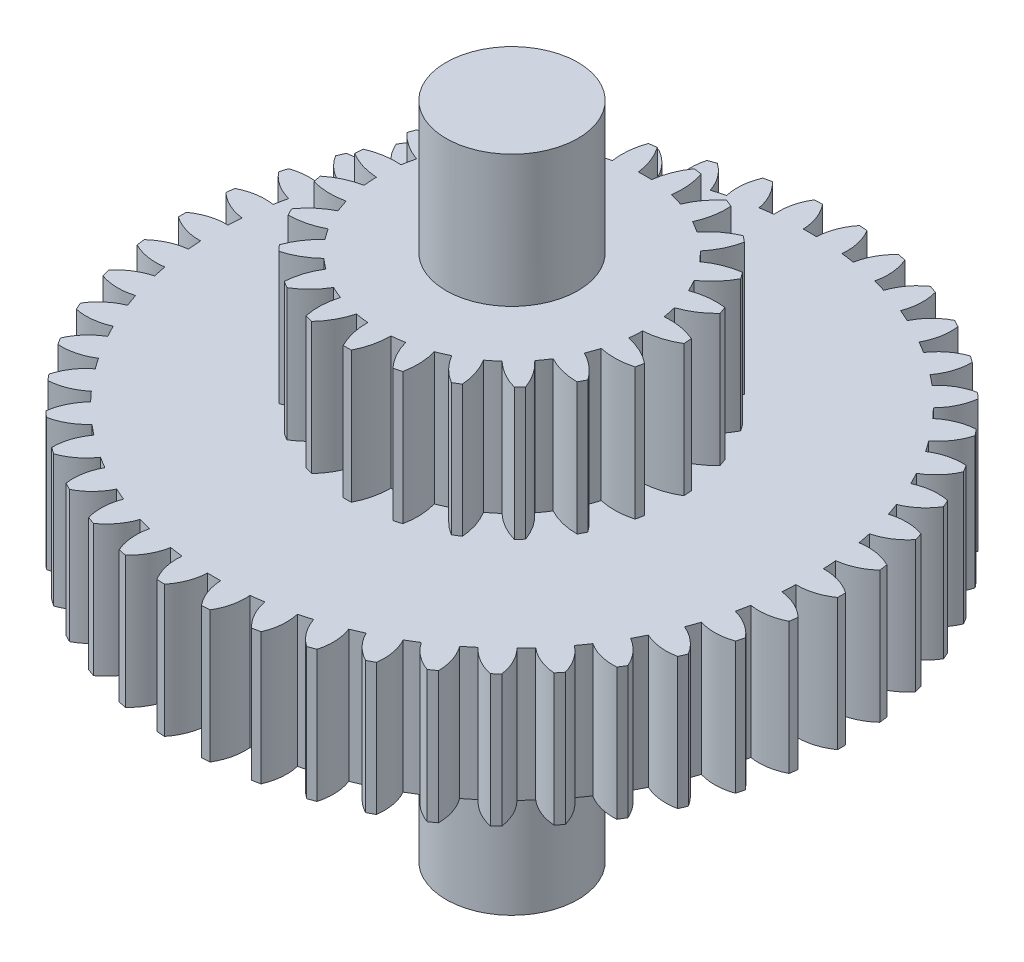
SolidWorks part; units mm, degrees
ref_plane "Front Plane" through (0, 0, 0) normal (0, 0, 1) x (1, 0, 0)
ref_plane "Top Plane" through (0, 0, 0) normal (0, 1, 0) x (1, 0, 0)
ref_plane "Right Plane" through (0, 0, 0) normal (1, 0, 0) x (0, 0, -1)
sketch "Sketch1" plane through (0, 0, 0) normal (0, 1, 0) x (1, 0, 0)
  arc A0 (-1.1228, 2.2337) -> (-1.1773, 2.2054) centre (0, 0) ccw
  arc A1 (-2.1122, 0.8038) -> (-2.1457, 0.7095) centre (0, 0) ccw
  arc A2 (0.05, 2.2594) -> (0.14, 2.4961) centre (0.4546, 2.241) cw
  arc A3 (-0.05, 2.2594) -> (-0.14, 2.4961) centre (-0.4546, 2.241) ccw
  arc A4 (0.3572, 2.2316) -> (0.4786, 2.4538) centre (0.7555, 2.1582) cw
  arc A5 (0.2581, 2.2452) -> (0.2012, 2.4919) centre (-0.1453, 2.282) ccw
  arc A6 (0.6577, 2.1622) -> (0.8082, 2.3657) centre (1.0424, 2.0352) cw
  arc A7 (0.5614, 2.1892) -> (0.5386, 2.4413) centre (0.1668, 2.2805) ccw
  arc A8 (0.946, 2.0525) -> (1.1228, 2.2337) centre (1.3098, 1.8743) cw
  arc A9 (0.8543, 2.0923) -> (0.866, 2.3452) centre (0.4758, 2.2366) ccw
  arc A10 (1.2167, 1.9045) -> (1.4165, 2.06) centre (1.5528, 1.6785) cw
  arc A11 (1.1313, 1.9565) -> (1.1773, 2.2054) centre (0.7759, 2.151) ccw
  arc A12 (1.4647, 1.7211) -> (1.6838, 1.8479) centre (1.7669, 1.4514) cw
  arc A13 (1.3871, 1.7842) -> (1.4666, 2.0246) centre (1.0616, 2.0253) ccw
  arc A14 (1.6854, 1.5057) -> (1.9198, 1.6014) centre (1.9481, 1.1973) cw
  arc A15 (1.6172, 1.5787) -> (1.7287, 1.806) centre (1.3275, 1.8619) ccw
  arc A16 (1.8747, 1.2621) -> (2.12, 1.3251) centre (2.093, 0.9209) cw
  arc A17 (1.8171, 1.3438) -> (1.9585, 1.5538) centre (1.5686, 1.6638) ccw
  arc A18 (2.0291, 0.9951) -> (2.2806, 1.0241) centre (2.1989, 0.6273) cw
  arc A19 (1.9831, 1.0839) -> (2.1518, 1.2727) centre (1.7806, 1.4347) ccw
  arc A20 (2.1457, 0.7095) -> (2.3988, 0.704) centre (2.2638, 0.3221) cw
  arc A21 (2.1122, 0.8038) -> (2.3051, 0.9678) centre (1.9593, 1.1788) ccw
  arc A22 (2.2224, 0.4107) -> (2.4724, 0.3708) centre (2.2866, 0.0108) cw
  arc A23 (2.202, 0.5087) -> (2.4154, 0.6449) centre (2.1016, 0.9011) ccw
  arc A24 (2.2576, 0.1043) -> (2.4998, 0.0307) centre (2.2668, -0.3006) cw
  arc A25 (2.2508, 0.2041) -> (2.4807, 0.31) centre (2.2047, 0.6065) ccw
  arc A26 (2.2508, -0.2041) -> (2.4807, -0.31) centre (2.2047, -0.6065) cw
  arc A27 (2.2576, -0.1043) -> (2.4998, -0.0307) centre (2.2668, 0.3006) ccw
  arc A28 (2.202, -0.5087) -> (2.4154, -0.6449) centre (2.1016, -0.9011) cw
  arc A29 (2.2224, -0.4107) -> (2.4724, -0.3708) centre (2.2866, -0.0108) ccw
  arc A30 (2.1122, -0.8038) -> (2.3051, -0.9678) centre (1.9593, -1.1788) cw
  arc A31 (2.1457, -0.7095) -> (2.3988, -0.704) centre (2.2638, -0.3221) ccw
  arc A32 (1.9831, -1.0839) -> (2.1518, -1.2727) centre (1.7806, -1.4347) cw
  arc A33 (2.0291, -0.9951) -> (2.2806, -1.0241) centre (2.1989, -0.6273) ccw
  arc A34 (1.8171, -1.3438) -> (1.9585, -1.5538) centre (1.5686, -1.6638) cw
  arc A35 (1.8747, -1.2621) -> (2.12, -1.3251) centre (2.093, -0.9209) ccw
  arc A36 (1.6172, -1.5787) -> (1.7287, -1.806) centre (1.3275, -1.8619) cw
  arc A37 (1.6854, -1.5057) -> (1.9198, -1.6014) centre (1.9481, -1.1973) ccw
  arc A38 (1.3871, -1.7842) -> (1.4666, -2.0246) centre (1.0616, -2.0253) cw
  arc A39 (1.4647, -1.7211) -> (1.6838, -1.8479) centre (1.7669, -1.4514) ccw
  arc A40 (1.1313, -1.9565) -> (1.1773, -2.2054) centre (0.7759, -2.151) cw
  arc A41 (1.2167, -1.9045) -> (1.4165, -2.06) centre (1.5528, -1.6785) ccw
  arc A42 (0.8543, -2.0923) -> (0.866, -2.3452) centre (0.4758, -2.2366) cw
  arc A43 (0.946, -2.0525) -> (1.1228, -2.2337) centre (1.3098, -1.8743) ccw
  arc A44 (0.5614, -2.1892) -> (0.5386, -2.4413) centre (0.1668, -2.2805) cw
  arc A45 (0.6577, -2.1622) -> (0.8082, -2.3657) centre (1.0424, -2.0352) ccw
  arc A46 (0.2581, -2.2452) -> (0.2012, -2.4919) centre (-0.1453, -2.282) cw
  arc A47 (0.3572, -2.2316) -> (0.4786, -2.4538) centre (0.7555, -2.1582) ccw
  arc A48 (-0.05, -2.2594) -> (-0.14, -2.4961) centre (-0.4546, -2.241) cw
  arc A49 (0.05, -2.2594) -> (0.14, -2.4961) centre (0.4546, -2.241) ccw
  arc A50 (-0.3572, -2.2316) -> (-0.4786, -2.4538) centre (-0.7555, -2.1582) cw
  arc A51 (-0.2581, -2.2452) -> (-0.2012, -2.4919) centre (0.1453, -2.282) ccw
  arc A52 (-0.6577, -2.1622) -> (-0.8082, -2.3657) centre (-1.0424, -2.0352) cw
  arc A53 (-0.5614, -2.1892) -> (-0.5386, -2.4413) centre (-0.1668, -2.2805) ccw
  arc A54 (-0.946, -2.0525) -> (-1.1228, -2.2337) centre (-1.3098, -1.8743) cw
  arc A55 (-0.8543, -2.0923) -> (-0.866, -2.3452) centre (-0.4758, -2.2366) ccw
  arc A56 (-1.2167, -1.9045) -> (-1.4165, -2.06) centre (-1.5528, -1.6785) cw
  arc A57 (-1.1313, -1.9565) -> (-1.1773, -2.2054) centre (-0.7759, -2.151) ccw
  arc A58 (-1.4647, -1.7211) -> (-1.6838, -1.8479) centre (-1.7669, -1.4514) cw
  arc A59 (-1.3871, -1.7842) -> (-1.4666, -2.0246) centre (-1.0616, -2.0253) ccw
  arc A60 (-1.6854, -1.5057) -> (-1.9198, -1.6014) centre (-1.9481, -1.1973) cw
  arc A61 (-1.6172, -1.5787) -> (-1.7287, -1.806) centre (-1.3275, -1.8619) ccw
  arc A62 (-1.8747, -1.2621) -> (-2.12, -1.3251) centre (-2.093, -0.9209) cw
  arc A63 (-1.8171, -1.3438) -> (-1.9585, -1.5538) centre (-1.5686, -1.6638) ccw
  arc A64 (-2.0291, -0.9951) -> (-2.2806, -1.0241) centre (-2.1989, -0.6273) cw
  arc A65 (-1.9831, -1.0839) -> (-2.1518, -1.2727) centre (-1.7806, -1.4347) ccw
  arc A66 (-2.1457, -0.7095) -> (-2.3988, -0.704) centre (-2.2638, -0.3221) cw
  arc A67 (-2.1122, -0.8038) -> (-2.3051, -0.9678) centre (-1.9593, -1.1788) ccw
  arc A68 (-2.2224, -0.4107) -> (-2.4724, -0.3708) centre (-2.2866, -0.0108) cw
  arc A69 (-2.202, -0.5087) -> (-2.4154, -0.6449) centre (-2.1016, -0.9011) ccw
  arc A70 (-2.2576, -0.1043) -> (-2.4998, -0.0307) centre (-2.2668, 0.3006) cw
  arc A71 (-2.2508, -0.2041) -> (-2.4807, -0.31) centre (-2.2047, -0.6065) ccw
  arc A72 (-2.2508, 0.2041) -> (-2.4807, 0.31) centre (-2.2047, 0.6065) cw
  arc A73 (-2.2576, 0.1043) -> (-2.4998, 0.0307) centre (-2.2668, -0.3006) ccw
  arc A74 (-2.202, 0.5087) -> (-2.4154, 0.6449) centre (-2.1016, 0.9011) cw
  arc A75 (-2.2224, 0.4107) -> (-2.4724, 0.3708) centre (-2.2866, 0.0108) ccw
  arc A76 (-2.1122, 0.8038) -> (-2.3051, 0.9678) centre (-1.9593, 1.1788) cw
  arc A77 (-2.1457, 0.7095) -> (-2.3988, 0.704) centre (-2.2638, 0.3221) ccw
  arc A78 (-1.9831, 1.0839) -> (-2.1518, 1.2727) centre (-1.7806, 1.4347) cw
  arc A79 (-2.0291, 0.9951) -> (-2.2806, 1.0241) centre (-2.1989, 0.6273) ccw
  arc A80 (-1.8171, 1.3438) -> (-1.9585, 1.5538) centre (-1.5686, 1.6638) cw
  arc A81 (-1.8747, 1.2621) -> (-2.12, 1.3251) centre (-2.093, 0.9209) ccw
  arc A82 (-1.6172, 1.5787) -> (-1.7287, 1.806) centre (-1.3275, 1.8619) cw
  arc A83 (-1.6854, 1.5057) -> (-1.9198, 1.6014) centre (-1.9481, 1.1973) ccw
  arc A84 (-1.3871, 1.7842) -> (-1.4666, 2.0246) centre (-1.0616, 2.0253) cw
  arc A85 (-1.4647, 1.7211) -> (-1.6838, 1.8479) centre (-1.7669, 1.4514) ccw
  arc A86 (-1.1313, 1.9565) -> (-1.1773, 2.2054) centre (-0.7759, 2.151) cw
  arc A87 (-1.2167, 1.9045) -> (-1.4165, 2.06) centre (-1.5528, 1.6785) ccw
  arc A88 (-0.8543, 2.0923) -> (-0.866, 2.3452) centre (-0.4758, 2.2366) cw
  arc A89 (-0.946, 2.0525) -> (-1.1228, 2.2337) centre (-1.3098, 1.8743) ccw
  arc A90 (-0.5614, 2.1892) -> (-0.5386, 2.4413) centre (-0.1668, 2.2805) cw
  arc A91 (-0.6577, 2.1622) -> (-0.8082, 2.3657) centre (-1.0424, 2.0352) ccw
  arc A92 (-0.2581, 2.2452) -> (-0.2012, 2.4919) centre (0.1453, 2.282) cw
  arc A93 (-0.3572, 2.2316) -> (-0.4786, 2.4538) centre (-0.7555, 2.1582) ccw
  arc A94 (-1.4165, 2.06) -> (-1.4666, 2.0246) centre (0, 0) ccw
  arc A95 (-1.6838, 1.8479) -> (-1.7287, 1.806) centre (0, 0) ccw
  arc A96 (-1.9198, 1.6014) -> (-1.9585, 1.5538) centre (0, 0) ccw
  arc A97 (-2.12, 1.3251) -> (-2.1518, 1.2727) centre (0, 0) ccw
  arc A98 (-2.2806, 1.0241) -> (-2.3051, 0.9678) centre (0, 0) ccw
  arc A99 (-2.3988, 0.704) -> (-2.4154, 0.6449) centre (0, 0) ccw
  arc A100 (-2.4724, 0.3708) -> (-2.4807, 0.31) centre (0, 0) ccw
  arc A101 (-2.4998, 0.0307) -> (-2.4998, -0.0307) centre (0, 0) ccw
  arc A102 (-2.4807, -0.31) -> (-2.4724, -0.3708) centre (0, 0) ccw
  arc A103 (-2.4154, -0.6449) -> (-2.3988, -0.704) centre (0, 0) ccw
  arc A104 (-2.3051, -0.9678) -> (-2.2806, -1.0241) centre (0, 0) ccw
  arc A105 (-2.1518, -1.2727) -> (-2.12, -1.3251) centre (0, 0) ccw
  arc A106 (-1.9585, -1.5538) -> (-1.9198, -1.6014) centre (0, 0) ccw
  arc A107 (-1.7287, -1.806) -> (-1.6838, -1.8479) centre (0, 0) ccw
  arc A108 (-1.4666, -2.0246) -> (-1.4165, -2.06) centre (0, 0) ccw
  arc A109 (-1.1773, -2.2054) -> (-1.1228, -2.2337) centre (0, 0) ccw
  arc A110 (-0.866, -2.3452) -> (-0.8082, -2.3657) centre (0, 0) ccw
  arc A111 (-0.5386, -2.4413) -> (-0.4786, -2.4538) centre (0, 0) ccw
  arc A112 (-0.2012, -2.4919) -> (-0.14, -2.4961) centre (0, 0) ccw
  arc A113 (0.14, -2.4961) -> (0.2012, -2.4919) centre (0, 0) ccw
  arc A114 (0.4786, -2.4538) -> (0.5386, -2.4413) centre (0, 0) ccw
  arc A115 (0.8082, -2.3657) -> (0.866, -2.3452) centre (0, 0) ccw
  arc A116 (1.1228, -2.2337) -> (1.1773, -2.2054) centre (0, 0) ccw
  arc A117 (1.4165, -2.06) -> (1.4666, -2.0246) centre (0, 0) ccw
  arc A118 (1.6838, -1.8479) -> (1.7287, -1.806) centre (0, 0) ccw
  arc A119 (1.9198, -1.6014) -> (1.9585, -1.5538) centre (0, 0) ccw
  arc A120 (2.12, -1.3251) -> (2.1518, -1.2727) centre (0, 0) ccw
  arc A121 (2.2806, -1.0241) -> (2.3051, -0.9678) centre (0, 0) ccw
  arc A122 (2.3988, -0.704) -> (2.4154, -0.6449) centre (0, 0) ccw
  arc A123 (2.4724, -0.3708) -> (2.4807, -0.31) centre (0, 0) ccw
  arc A124 (2.4998, -0.0307) -> (2.4998, 0.0307) centre (0, 0) ccw
  arc A125 (2.4807, 0.31) -> (2.4724, 0.3708) centre (0, 0) ccw
  arc A126 (2.4154, 0.6449) -> (2.3988, 0.704) centre (0, 0) ccw
  arc A127 (2.3051, 0.9678) -> (2.2806, 1.0241) centre (0, 0) ccw
  arc A128 (2.1518, 1.2727) -> (2.12, 1.3251) centre (0, 0) ccw
  arc A129 (1.9585, 1.5538) -> (1.9198, 1.6014) centre (0, 0) ccw
  arc A130 (1.7287, 1.806) -> (1.6838, 1.8479) centre (0, 0) ccw
  arc A131 (1.4666, 2.0246) -> (1.4165, 2.06) centre (0, 0) ccw
  arc A132 (1.1773, 2.2054) -> (1.1228, 2.2337) centre (0, 0) ccw
  arc A133 (0.866, 2.3452) -> (0.8082, 2.3657) centre (0, 0) ccw
  arc A134 (0.5386, 2.4413) -> (0.4786, 2.4538) centre (0, 0) ccw
  arc A135 (0.2012, 2.4919) -> (0.14, 2.4961) centre (0, 0) ccw
  arc A136 (-0.14, 2.4961) -> (-0.2012, 2.4919) centre (0, 0) ccw
  arc A137 (-0.4786, 2.4538) -> (-0.5386, 2.4413) centre (0, 0) ccw
  arc A138 (-0.8082, 2.3657) -> (-0.866, 2.3452) centre (0, 0) ccw
  arc A139 (-2.202, 0.5087) -> (-2.2224, 0.4107) centre (0, 0) ccw
  arc A140 (-2.2508, 0.2041) -> (-2.2576, 0.1043) centre (0, 0) ccw
  arc A141 (-2.2576, -0.1043) -> (-2.2508, -0.2041) centre (0, 0) ccw
  arc A142 (-2.2224, -0.4107) -> (-2.202, -0.5087) centre (0, 0) ccw
  arc A143 (-2.1457, -0.7095) -> (-2.1122, -0.8038) centre (0, 0) ccw
  arc A144 (-2.0291, -0.9951) -> (-1.9831, -1.0839) centre (0, 0) ccw
  arc A145 (-1.8747, -1.2621) -> (-1.8171, -1.3438) centre (0, 0) ccw
  arc A146 (-1.6854, -1.5057) -> (-1.6172, -1.5787) centre (0, 0) ccw
  arc A147 (-1.4647, -1.7211) -> (-1.3871, -1.7842) centre (0, 0) ccw
  arc A148 (-1.2167, -1.9045) -> (-1.1313, -1.9565) centre (0, 0) ccw
  arc A149 (-0.946, -2.0525) -> (-0.8543, -2.0923) centre (0, 0) ccw
  arc A150 (-0.6577, -2.1622) -> (-0.5614, -2.1892) centre (0, 0) ccw
  arc A151 (-0.3572, -2.2316) -> (-0.2581, -2.2452) centre (0, 0) ccw
  arc A152 (-0.05, -2.2594) -> (0.05, -2.2594) centre (0, 0) ccw
  arc A153 (0.2581, -2.2452) -> (0.3572, -2.2316) centre (0, 0) ccw
  arc A154 (0.5614, -2.1892) -> (0.6577, -2.1622) centre (0, 0) ccw
  arc A155 (0.8543, -2.0923) -> (0.946, -2.0525) centre (0, 0) ccw
  arc A156 (1.1313, -1.9565) -> (1.2167, -1.9045) centre (0, 0) ccw
  arc A157 (1.3871, -1.7842) -> (1.4647, -1.7211) centre (0, 0) ccw
  arc A158 (1.6172, -1.5787) -> (1.6854, -1.5057) centre (0, 0) ccw
  arc A159 (1.8171, -1.3438) -> (1.8747, -1.2621) centre (0, 0) ccw
  arc A160 (1.9831, -1.0839) -> (2.0291, -0.9951) centre (0, 0) ccw
  arc A161 (2.1122, -0.8038) -> (2.1457, -0.7095) centre (0, 0) ccw
  arc A162 (2.202, -0.5087) -> (2.2224, -0.4107) centre (0, 0) ccw
  arc A163 (2.2508, -0.2041) -> (2.2576, -0.1043) centre (0, 0) ccw
  arc A164 (2.2576, 0.1043) -> (2.2508, 0.2041) centre (0, 0) ccw
  arc A165 (2.2224, 0.4107) -> (2.202, 0.5087) centre (0, 0) ccw
  arc A166 (2.1457, 0.7095) -> (2.1122, 0.8038) centre (0, 0) ccw
  arc A167 (2.0291, 0.9951) -> (1.9831, 1.0839) centre (0, 0) ccw
  arc A168 (1.8747, 1.2621) -> (1.8171, 1.3438) centre (0, 0) ccw
  arc A169 (1.6854, 1.5057) -> (1.6172, 1.5787) centre (0, 0) ccw
  arc A170 (1.4647, 1.7211) -> (1.3871, 1.7842) centre (0, 0) ccw
  arc A171 (1.2167, 1.9045) -> (1.1313, 1.9565) centre (0, 0) ccw
  arc A172 (0.946, 2.0525) -> (0.8543, 2.0923) centre (0, 0) ccw
  arc A173 (0.6577, 2.1622) -> (0.5614, 2.1892) centre (0, 0) ccw
  arc A174 (0.3572, 2.2316) -> (0.2581, 2.2452) centre (0, 0) ccw
  arc A175 (0.05, 2.2594) -> (-0.05, 2.2594) centre (0, 0) ccw
  arc A176 (-1.3871, 1.7842) -> (-1.4647, 1.7211) centre (0, 0) ccw
  arc A177 (-1.1313, 1.9565) -> (-1.2167, 1.9045) centre (0, 0) ccw
  arc A178 (-0.8543, 2.0923) -> (-0.946, 2.0525) centre (0, 0) ccw
  arc A179 (-0.5614, 2.1892) -> (-0.6577, 2.1622) centre (0, 0) ccw
  arc A180 (-0.2581, 2.2452) -> (-0.3572, 2.2316) centre (0, 0) ccw
  arc A181 (-1.6172, 1.5787) -> (-1.6854, 1.5057) centre (0, 0) ccw
  arc A182 (-1.8171, 1.3438) -> (-1.8747, 1.2621) centre (0, 0) ccw
  arc A183 (-1.9831, 1.0839) -> (-2.0291, 0.9951) centre (0, 0) ccw
  point P4 (0, 2.26)
  point P5 (0, 2.5)
  point P285 (0, 0)
  dimension "D1" = 5
  dimension "D2" = 0.24
  dimension "D5" = 46
extrude "Boss-Extrude1" add sketch "Sketch1" along normal blind 1
sketch "Sketch2" plane through (0, 0, 0) normal (0, -1, 0) x (1, 0, 0)
  circle A0 centre (0, 0) radius 0.5
  dimension "D1" = 1
extrude "Boss-Extrude2" add sketch "Sketch2" along normal blind 2 and the other way blind 3
sketch "Sketch3" plane through (0, 1, 0) normal (0, 1, 0) x (1, 0, 0)
  arc A0 (-0.765, 0.9886) -> (-0.8122, 0.9501) centre (0, 0) ccw
  arc A1 (-0.4814, 0.8879) -> (-0.5669, 0.8359) centre (0, 0) ccw
  arc A2 (0.05, 1.0088) -> (0.14, 1.2421) centre (0.5621, 0.9453) cw
  arc A3 (-0.05, 1.0088) -> (-0.14, 1.2421) centre (-0.5621, 0.9453) ccw
  arc A4 (0.3203, 0.9579) -> (0.4699, 1.1583) centre (0.7963, 0.7586) cw
  arc A5 (0.224, 0.9848) -> (0.2003, 1.2338) centre (-0.2862, 1.0619) ccw
  arc A6 (0.5669, 0.8359) -> (0.765, 0.9886) centre (0.9714, 0.5157) cw
  arc A7 (0.4814, 0.8879) -> (0.5258, 1.134) centre (0.0109, 1.0997) ccw
  arc A8 (0.7714, 0.652) -> (1.0034, 0.7455) centre (1.0745, 0.2345) cw
  arc A9 (0.7031, 0.7251) -> (0.8122, 0.9501) centre (0.3072, 1.056) ccw
  arc A10 (0.9187, 0.4197) -> (1.1673, 0.4472) centre (1.0979, -0.0641) cw
  arc A11 (0.8727, 0.5085) -> (1.0385, 0.6958) centre (0.5808, 0.934) ccw
  arc A12 (0.9978, 0.1563) -> (1.2446, 0.1156) centre (1.0399, -0.358) cw
  arc A13 (0.9775, 0.2542) -> (1.1877, 0.3898) centre (0.8112, 0.7426) ccw
  arc A14 (1.003, -0.1187) -> (1.2297, -0.2244) centre (0.9048, -0.6253) cw
  arc A15 (1.0098, -0.019) -> (1.2488, 0.0549) centre (0.9815, 0.4962) ccw
  arc A16 (0.9338, -0.3849) -> (1.1235, -0.5479) centre (0.7025, -0.8462) cw
  arc A17 (0.9673, -0.2907) -> (1.2173, -0.284) centre (1.079, 0.213) ccw
  arc A18 (0.7953, -0.6226) -> (0.9341, -0.8307) centre (0.4482, -1.0043) cw
  arc A19 (0.853, -0.5409) -> (1.0955, -0.6019) centre (1.0964, -0.086) ccw
  arc A20 (0.5978, -0.8141) -> (0.6753, -1.0519) centre (0.1606, -1.088) cw
  arc A21 (0.6754, -0.751) -> (0.8925, -0.8752) centre (1.0326, -0.3786) ccw
  arc A22 (0.356, -0.9452) -> (0.3665, -1.1951) centre (-0.1389, -1.091) cw
  arc A23 (0.4478, -0.9053) -> (0.6233, -1.0835) centre (0.8922, -0.6431) ccw
  arc A24 (0.0878, -1.0062) -> (0.0304, -1.2496) centre (-0.4281, -1.0131) cw
  arc A25 (0.1869, -0.9926) -> (0.3078, -1.2115) centre (0.6856, -0.86) ccw
  arc A26 (-0.1869, -0.9926) -> (-0.3078, -1.2115) centre (-0.6856, -0.86) cw
  arc A27 (-0.0878, -1.0062) -> (-0.0304, -1.2496) centre (0.4281, -1.0131) ccw
  arc A28 (-0.4478, -0.9053) -> (-0.6233, -1.0835) centre (-0.8922, -0.6431) cw
  arc A29 (-0.356, -0.9452) -> (-0.3665, -1.1951) centre (0.1389, -1.091) ccw
  arc A30 (-0.6754, -0.751) -> (-0.8925, -0.8752) centre (-1.0326, -0.3786) cw
  arc A31 (-0.5978, -0.8141) -> (-0.6753, -1.0519) centre (-0.1606, -1.088) ccw
  arc A32 (-0.853, -0.5409) -> (-1.0955, -0.6019) centre (-1.0964, -0.086) cw
  arc A33 (-0.7953, -0.6226) -> (-0.9341, -0.8307) centre (-0.4482, -1.0043) ccw
  arc A34 (-0.9673, -0.2907) -> (-1.2173, -0.284) centre (-1.079, 0.213) cw
  arc A35 (-0.9338, -0.3849) -> (-1.1235, -0.5479) centre (-0.7025, -0.8462) ccw
  arc A36 (-1.0098, -0.019) -> (-1.2488, 0.0549) centre (-0.9815, 0.4962) cw
  arc A37 (-1.003, -0.1187) -> (-1.2297, -0.2244) centre (-0.9048, -0.6253) ccw
  arc A38 (-0.9775, 0.2542) -> (-1.1877, 0.3898) centre (-0.8112, 0.7426) cw
  arc A39 (-0.9978, 0.1563) -> (-1.2446, 0.1156) centre (-1.0399, -0.358) ccw
  arc A40 (-0.8727, 0.5085) -> (-1.0385, 0.6958) centre (-0.5808, 0.934) cw
  arc A41 (-0.9187, 0.4197) -> (-1.1673, 0.4472) centre (-1.0979, -0.0641) ccw
  arc A42 (-0.7031, 0.7251) -> (-0.8122, 0.9501) centre (-0.3072, 1.056) cw
  arc A43 (-0.7714, 0.652) -> (-1.0034, 0.7455) centre (-1.0745, 0.2345) ccw
  arc A44 (-0.4814, 0.8879) -> (-0.5258, 1.134) centre (-0.0109, 1.0997) cw
  arc A45 (-0.5669, 0.8359) -> (-0.765, 0.9886) centre (-0.9714, 0.5157) ccw
  arc A46 (-0.224, 0.9848) -> (-0.2003, 1.2338) centre (0.2862, 1.0619) cw
  arc A47 (-0.3203, 0.9579) -> (-0.4699, 1.1583) centre (-0.7963, 0.7586) ccw
  arc A48 (-1.0034, 0.7455) -> (-1.0385, 0.6958) centre (0, 0) ccw
  arc A49 (-1.2446, 0.1156) -> (-1.2488, 0.0549) centre (0, 0) ccw
  arc A50 (-1.1673, 0.4472) -> (-1.1877, 0.3898) centre (0, 0) ccw
  arc A51 (-1.2297, -0.2244) -> (-1.2173, -0.284) centre (0, 0) ccw
  arc A52 (-1.1235, -0.5479) -> (-1.0955, -0.6019) centre (0, 0) ccw
  arc A53 (-0.9341, -0.8307) -> (-0.8925, -0.8752) centre (0, 0) ccw
  arc A54 (-0.3665, -1.1951) -> (-0.3078, -1.2115) centre (0, 0) ccw
  arc A55 (-0.6753, -1.0519) -> (-0.6233, -1.0835) centre (0, 0) ccw
  arc A56 (-0.0304, -1.2496) -> (0.0304, -1.2496) centre (0, 0) ccw
  arc A57 (0.6233, -1.0835) -> (0.6753, -1.0519) centre (0, 0) ccw
  arc A58 (0.8925, -0.8752) -> (0.9341, -0.8307) centre (0, 0) ccw
  arc A59 (0.3078, -1.2115) -> (0.3665, -1.1951) centre (0, 0) ccw
  arc A60 (1.2173, -0.284) -> (1.2297, -0.2244) centre (0, 0) ccw
  arc A61 (1.0955, -0.6019) -> (1.1235, -0.5479) centre (0, 0) ccw
  arc A62 (1.2488, 0.0549) -> (1.2446, 0.1156) centre (0, 0) ccw
  arc A63 (1.1877, 0.3898) -> (1.1673, 0.4472) centre (0, 0) ccw
  arc A64 (1.0385, 0.6958) -> (1.0034, 0.7455) centre (0, 0) ccw
  arc A65 (0.8122, 0.9501) -> (0.765, 0.9886) centre (0, 0) ccw
  arc A66 (0.5258, 1.134) -> (0.4699, 1.1583) centre (0, 0) ccw
  arc A67 (0.2003, 1.2338) -> (0.14, 1.2421) centre (0, 0) ccw
  arc A68 (-0.4699, 1.1583) -> (-0.5258, 1.134) centre (0, 0) ccw
  arc A69 (-0.14, 1.2421) -> (-0.2003, 1.2338) centre (0, 0) ccw
  arc A70 (-0.7031, 0.7251) -> (-0.7714, 0.652) centre (0, 0) ccw
  arc A71 (-0.9775, 0.2542) -> (-0.9978, 0.1563) centre (0, 0) ccw
  arc A72 (-1.0098, -0.019) -> (-1.003, -0.1187) centre (0, 0) ccw
  arc A73 (-0.9673, -0.2907) -> (-0.9338, -0.3849) centre (0, 0) ccw
  arc A74 (-0.853, -0.5409) -> (-0.7953, -0.6226) centre (0, 0) ccw
  arc A75 (-0.224, 0.9848) -> (-0.3203, 0.9579) centre (0, 0) ccw
  arc A76 (0.05, 1.0088) -> (-0.05, 1.0088) centre (0, 0) ccw
  arc A77 (0.3203, 0.9579) -> (0.224, 0.9848) centre (0, 0) ccw
  arc A78 (0.5669, 0.8359) -> (0.4814, 0.8879) centre (0, 0) ccw
  arc A79 (0.7714, 0.652) -> (0.7031, 0.7251) centre (0, 0) ccw
  arc A80 (0.9187, 0.4197) -> (0.8727, 0.5085) centre (0, 0) ccw
  arc A81 (0.9978, 0.1563) -> (0.9775, 0.2542) centre (0, 0) ccw
  arc A82 (1.003, -0.1187) -> (1.0098, -0.019) centre (0, 0) ccw
  arc A83 (0.9338, -0.3849) -> (0.9673, -0.2907) centre (0, 0) ccw
  arc A84 (0.7953, -0.6226) -> (0.853, -0.5409) centre (0, 0) ccw
  arc A85 (0.5978, -0.8141) -> (0.6754, -0.751) centre (0, 0) ccw
  arc A86 (0.356, -0.9452) -> (0.4478, -0.9053) centre (0, 0) ccw
  arc A87 (0.0878, -1.0062) -> (0.1869, -0.9926) centre (0, 0) ccw
  arc A88 (-0.1869, -0.9926) -> (-0.0878, -1.0062) centre (0, 0) ccw
  arc A89 (-0.4478, -0.9053) -> (-0.356, -0.9452) centre (0, 0) ccw
  arc A90 (-0.6754, -0.751) -> (-0.5978, -0.8141) centre (0, 0) ccw
  arc A91 (-0.8727, 0.5085) -> (-0.9187, 0.4197) centre (0, 0) ccw
  point P4 (0, 1.25)
  point P5 (0, 1.01)
  point P147 (0, 0)
  dimension "D1" = 2.5
  dimension "D2" = 0.24
  dimension "D5" = 23
extrude "Boss-Extrude3" add sketch "Sketch3" along normal blind 1 contours A30 A90 A31 A55 A28 A89 A29 A54 A26 A88 A27 A56 A24 A87 A25 A59 A22 A86 A23 A57 A20 A85 A21 A58 A18 A84 A19 A61 A16 A83 A17 A60 A14 A82 A15 A62 A12 A81 A13 A63 A10 A80 A11 A64 A8 A79 A9 A65 A6 A78 A7
scale "Scale1" bodies to scale 103 scale about origin uniform scaling yes scale factor 2
sketch "Sketch4" plane through (0, -4, 0) normal (0, -1, 0) x (1, 0, 0)
  line L0 (-0.75, 0) -> (-0.75, -0.6614)
  line L1 (-0.75, 0) -> (-0.75, 0.6614)
  circle A0 centre (0, 0) radius 1 construction
  circle A1 centre (0, 0) radius 1 construction
  arc A2 (-0.75, 0.6614) -> (-0.75, -0.6614) centre (0, 0) ccw
  dimension "D1" = 0.75
extrude "Cut-Extrude1" cut sketch "Sketch4" against normal blind 2.5
